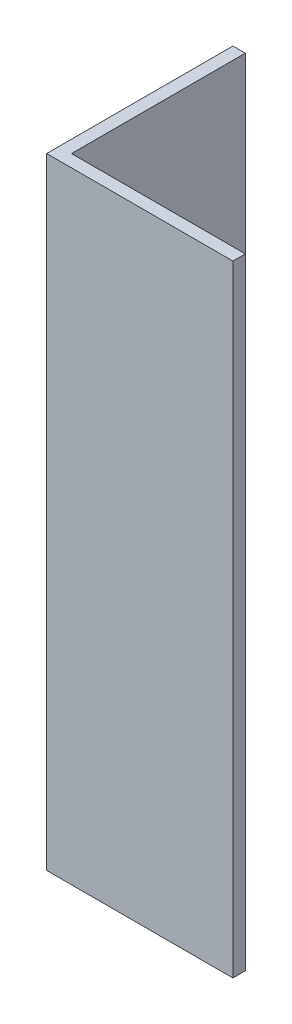
SolidWorks part; units mm, degrees
material "1060 Сплав"
ref_plane "Спереди" through (0, 0, 0) normal (0, 0, 1) x (1, 0, 0)
ref_plane "Сверху" through (0, 0, 0) normal (0, 1, 0) x (1, 0, 0)
ref_plane "Справа" through (0, 0, 0) normal (1, 0, 0) x (0, 0, -1)
sketch "Эскиз1" plane through (0, 0, 0) normal (0, 1, 0) x (1, 0, 0)
  line L0 (0, 0) -> (0, 15)
  line L1 (0, 15) -> (1, 15)
  line L2 (1, 15) -> (1, 1)
  line L3 (1, 1) -> (15, 1)
  line L4 (15, 1) -> (15, 0)
  line L5 (15, 0) -> (0, 0)
  dimension "D1" = 1
  dimension "D2" = 15
extrude "Бобышка-Вытянуть1" add sketch "Эскиз1" along normal blind 50
